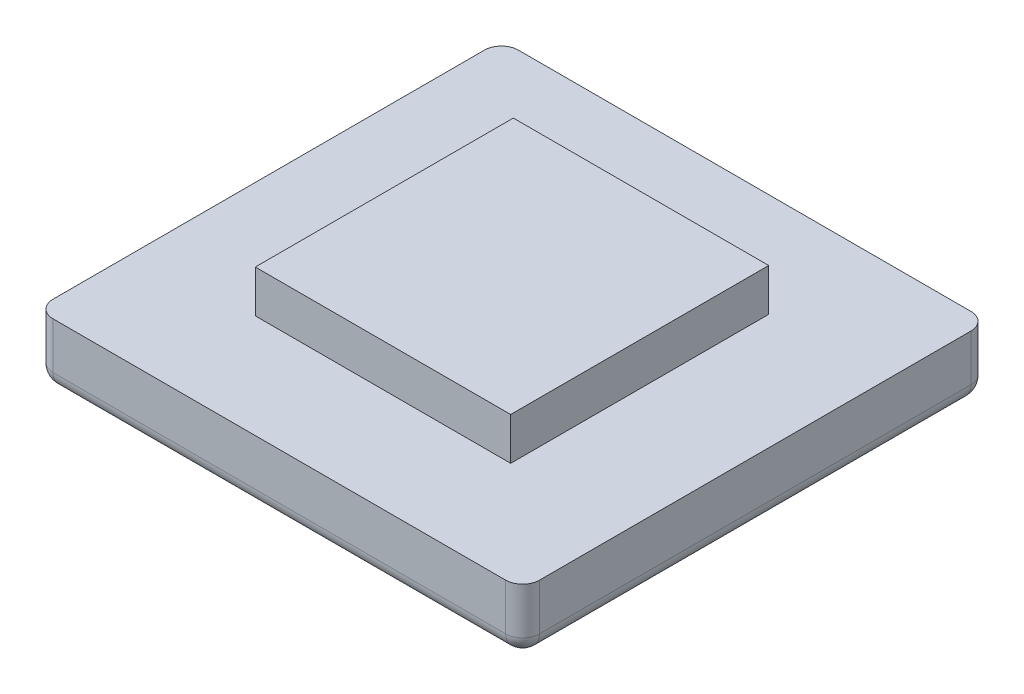
SolidWorks part; units mm, degrees
ref_plane "Front Plane" through (0, 0, 0) normal (0, 0, 1) x (1, 0, 0)
ref_plane "Top Plane" through (0, 0, 0) normal (0, 1, 0) x (1, 0, 0)
ref_plane "Right Plane" through (0, 0, 0) normal (1, 0, 0) x (0, 0, -1)
sketch "Sketch2" plane through (0, 0, 0) normal (0, 1, 0) x (1, 0, 0)
  line L1 (-21.1351, -53.8986) -> (93.8649, -53.8986)
  line L2 (-21.1351, -53.8986) -> (-21.1351, 56.1014)
  line L3 (-21.1351, 56.1014) -> (93.8649, 56.1014)
  line L4 (93.8649, -53.8986) -> (93.8649, 56.1014)
  dimension "D1" = 115
  dimension "D2" = 110
extrude "Boss-Extrude1" add sketch "Sketch2" along normal blind 15
sketch "Sketch3" plane through (0, 15, 0) normal (0, 1, 0) x (1, 0, 0)
  line L0 (93.8649, -53.8986) -> (93.8649, 56.1014) construction
  line L1 (6.1821, -29.3926) -> (66.5477, -29.3926)
  line L2 (6.1821, -29.3926) -> (6.1821, 31.5953)
  line L3 (6.1821, 31.5953) -> (66.5477, 31.5953)
  line L4 (66.5477, -29.3926) -> (66.5477, 31.5953)
  line L5 (6.1821, -29.3926) -> (66.5477, 31.5953) construction
  line L6 (6.1821, 31.5953) -> (66.5477, -29.3926) construction
  line L7 (93.8649, 56.1014) -> (-21.1351, 56.1014) construction
  point P0 (36.3649, 1.1014)
  dimension "D1" = 57.5
  dimension "D2" = 55
  dimension "D3" = 60.9879
extrude "Boss-Extrude2" add sketch "Sketch3" along normal blind 10
fillet "Fillet2" radius 4 8 edges at (36.3649, 0, 53.8986) (93.8649, 0, -1.1014) (36.3649, 0, -56.1014) (-21.1351, 0, -1.1014) (93.8649, 7.5, -56.1014) (93.8649, 7.5, 53.8986) (-21.1351, 7.5, 53.8986) (-21.1351, 7.5, -56.1014)
